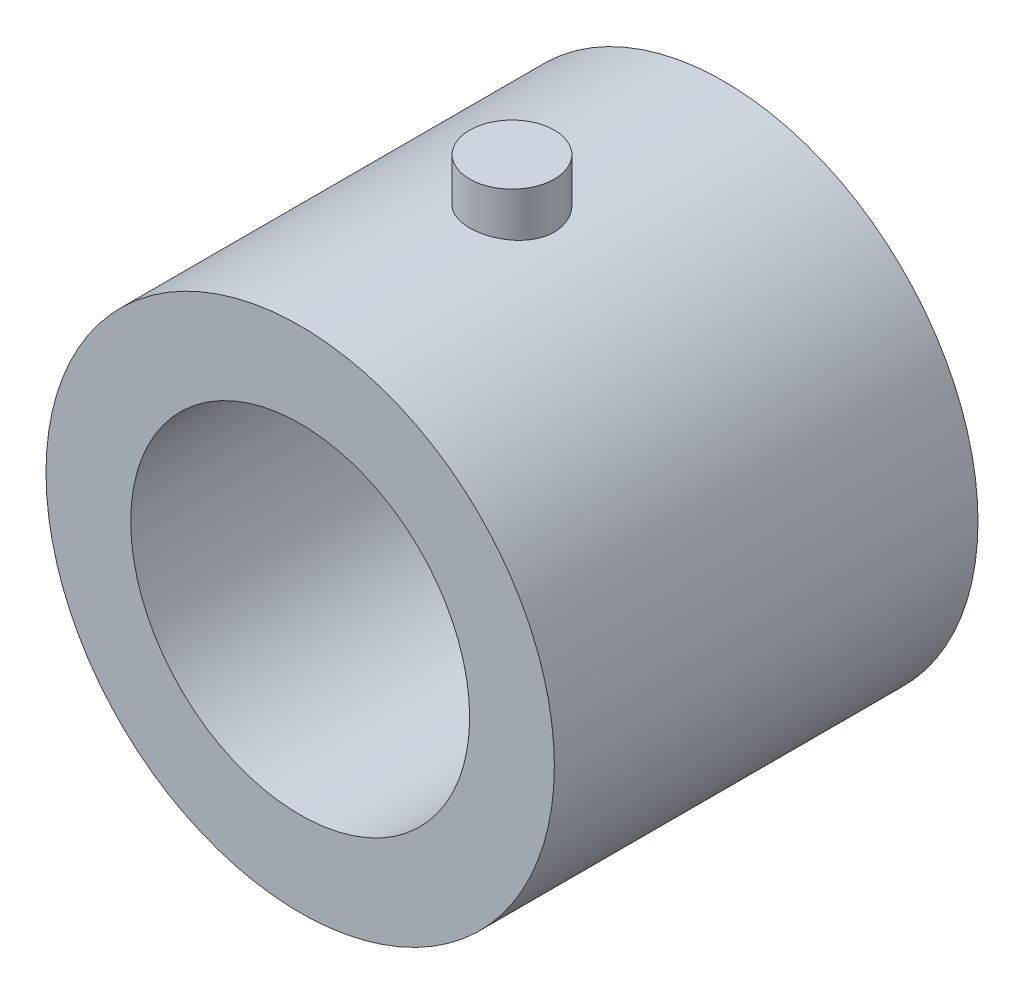
SolidWorks part; units mm, degrees
ref_plane "前视基准面" through (0, 0, 0) normal (0, 0, 1) x (1, 0, 0)
ref_plane "上视基准面" through (0, 0, 0) normal (0, 1, 0) x (1, 0, 0)
ref_plane "右视基准面" through (0, 0, 0) normal (1, 0, 0) x (0, 0, -1)
sketch "草图1" plane through (0, 0, 0) normal (0, 0, 1) x (1, 0, 0)
  circle A0 centre (0, 0) radius 3
  circle A1 centre (0, 0) radius 2
extrude "凸台-拉伸1" add sketch "草图1" along normal blind 5
sketch "草图2" plane through (0, 0, 0) normal (0, 1, 0) x (1, 0, 0)
  line L0 (-3, 0) -> (3, -5) construction
  circle A0 centre (0, -2.5) radius 0.5
extrude "凸台-拉伸2" add sketch "草图2" along normal blind 3.5
sketch "草图3" plane through (0, 0, 5) normal (0, 0, 1) x (1, 0, 0)
  circle A0 centre (0, 0) radius 2
extrude "切除-拉伸1" cut sketch "草图3" against normal blind 3.5
